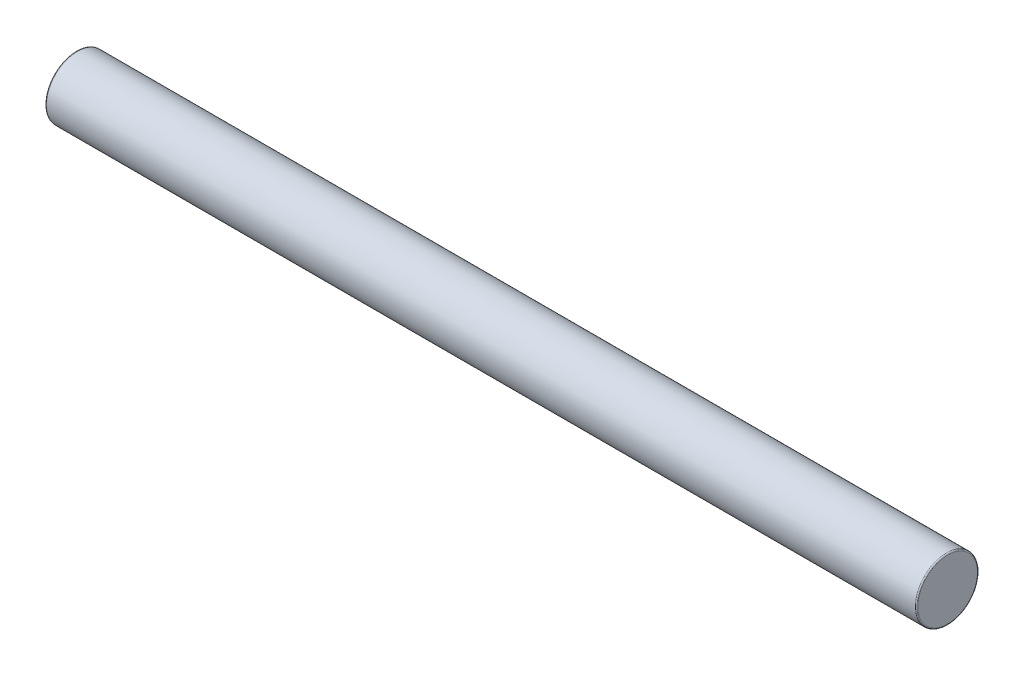
SolidWorks part; units mm, degrees
ref_plane "Alzado" through (0, 0, 0) normal (0, 0, 1) x (1, 0, 0)
ref_plane "Planta" through (0, 0, 0) normal (0, 1, 0) x (1, 0, 0)
ref_plane "Vista lateral" through (0, 0, 0) normal (1, 0, 0) x (0, 0, -1)
sketch "Croquis1" plane through (0, 0, 0) normal (1, 0, 0) x (0, 0, -1)
  circle A0 centre (0, 0) radius 5
  dimension "D1" = 10
extrude "Saliente-Extruir1" add sketch "Croquis1" along normal blind 140
fillet "Redondeo1" radius 0.2 2 edges at (0, 0, -5) (140, 0, -5)
